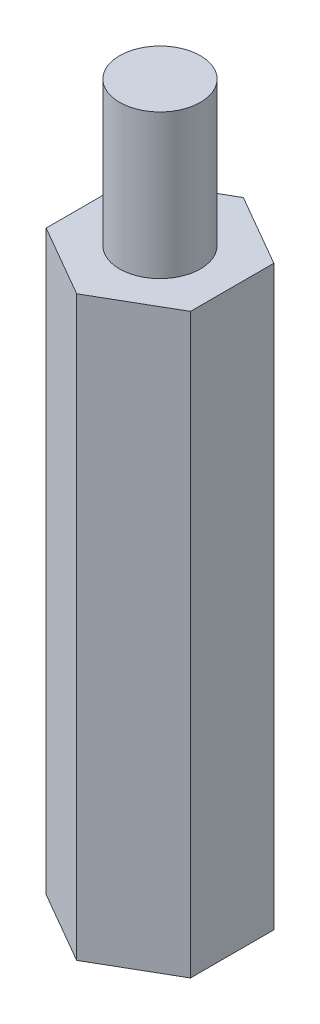
SolidWorks part; units mm, degrees
ref_plane "Front Plane" through (0, 0, 0) normal (0, 0, 1) x (1, 0, 0)
ref_plane "Top Plane" through (0, 0, 0) normal (0, 1, 0) x (1, 0, 0)
ref_plane "Right Plane" through (0, 0, 0) normal (1, 0, 0) x (0, 0, -1)
sketch "Sketch1" plane through (0, 0, 0) normal (0, 1, 0) x (1, 0, 0)
  line L1 (0, 3.6662) -> (-3.175, 1.8331)
  line L2 (-3.175, 1.8331) -> (-3.175, -1.8331)
  line L3 (-3.175, -1.8331) -> (0, -3.6662)
  line L4 (0, -3.6662) -> (3.175, -1.8331)
  line L5 (3.175, -1.8331) -> (3.175, 1.8331)
  line L6 (3.175, 1.8331) -> (0, 3.6662)
  circle A0 centre (0, 0) radius 3.175 construction
  dimension "D1" = 6.35
extrude "Boss-Extrude1" add sketch "Sketch1" along normal blind 25.4
sketch "Sketch2" plane through (0, 25.4, 0) normal (0, 1, 0) x (1, 0, 0)
  circle A0 centre (0, 0) radius 1.778
extrude "Boss-Extrude2" add sketch "Sketch2" along normal blind 6.35
